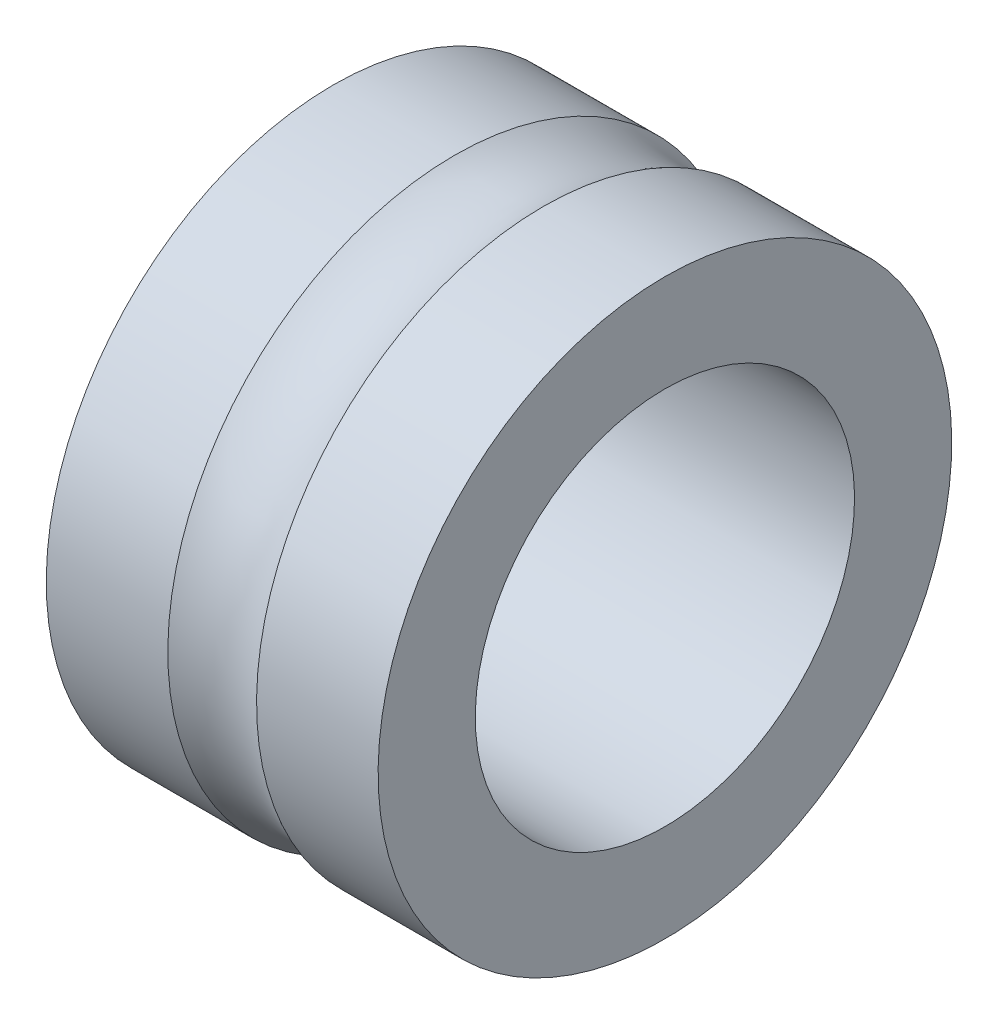
SolidWorks part; units mm, degrees
ref_plane "Front Plane" through (0, 0, 0) normal (0, 0, 1) x (1, 0, 0)
ref_plane "Top Plane" through (0, 0, 0) normal (0, 1, 0) x (1, 0, 0)
ref_plane "Right Plane" through (0, 0, 0) normal (1, 0, 0) x (0, 0, -1)
sketch "Sketch2" plane through (0, 0, 0) normal (0, 0, 1) x (1, 0, 0)
  line L0 (23.6602, 0) -> (-21.7547, 0) construction
  line L1 (3.5, 11) -> (-3.5, 11)
  line L2 (3.5, 11) -> (3.5, 9.6)
  line L3 (3.5, 9.6) -> (-3.5, 9.6)
  line L4 (-3.5, 9.6) -> (-3.5, 11)
  line L5 (3.5, 6.05) -> (3.5, 4)
  line L6 (3.5, 4) -> (-3.5, 4)
  line L7 (-3.5, 4) -> (-3.5, 6.05)
  line L8 (-3.5, 6.05) -> (3.5, 6.05)
  circle A0 centre (0, 7.8) radius 1.9845
  point P9 (0, 11)
  dimension "D1" = 1.75
  dimension "Ball Bearing Size" = 3.969
  dimension "Bearing Width" = 7
  dimension "Inner Casing Inner" = 4
  dimension "Inner Casing Outter" = 6.05
  dimension "Outter Casing Inner" = 9.6
  dimension "Outter Case Outter" = 11
revolve "Revolve1" add sketch "Sketch2" angle 360 about L0
sketch "Sketch3" plane through (0, 0, 0) normal (1, 0, 0) x (0, 0, -1)
  circle A0 centre (0, 0) radius 7.8
  dimension "Ball Track" = 15.6
sketch "Sketch4" plane through (0, 0, 0) normal (0, 0, 1) x (1, 0, 0)
  line L0 (-6.5669, 0) -> (7.975, 0) construction
equation "\"Motor Width\"= 42.3'eg: For stepper motor Nema 17 = 42.3mm"
equation "\"Motor Hole Config Width\"= 31'eg: For stepper motor Nema 17 = 31"
equation "\"Mounting Hole Diameter\"= 3'eg: For Nema 17 3mm"
equation "\"Motor Depth\"= 50'eg: For Nema 17 50mm"
equation "\"Exposed Shaft Length\"= 22'eg: For Nema 17 22mm"
equation "\"Shaft Seround Depthr\"= 2'eg: For Nema 17 2mm"
equation "\"Shaft Diameter\"= 5'eg: For Nema 17 5mm"
equation "\"Top/Bottom Casing Depth\"= 10'Guess"
equation "\"Mid Casing Depth\"= \"Motor Depth\" - 2 * ( \"Top/Bottom Casing Depth\" )"
equation "\"Bearing Outter Diameter\"= 22' From Spec 608z = 22mm"
equation "\"Shaft Clearance Hole\"= \"Shaft Diameter\"+1.5'Guess"
equation "\"Bearing Ball Size\"= 3.969'From Spec"
equation "\"Bearing Inner Case Inner Diameter\"= 8'From Spec"
equation "\"Bearing Inner Case Outter Diameter\"= 12.1'From Spec"
equation "\"Bearing Outter Case Inner Diameter\"= 19.2'From Spec"
equation "\"Bearing Width\"= 7'From Spec"
equation "\"Bearing Width@Sketch2\"=\"Bearing Width\""
equation "\"Inner Casing Inner@Sketch2\"=\"Bearing Inner Case Inner Diameter\"/2"
equation "\"Inner Casing Outter@Sketch2\"=\"Bearing Inner Case Outter Diameter\"/2"
equation "\"Outter Casing Inner@Sketch2\"=\"Bearing Outter Case Inner Diameter\"/2"
equation "\"Outter Case Outter@Sketch2\"=\"Bearing Outter Diameter\"/2"
equation "\"Ball Bearing Size@Sketch2\"=\"Bearing Ball Size\""
equation "\"Ball Track@Sketch3\"=\"Bearing Inner Case Outter Diameter\"+2*(1.75)"
